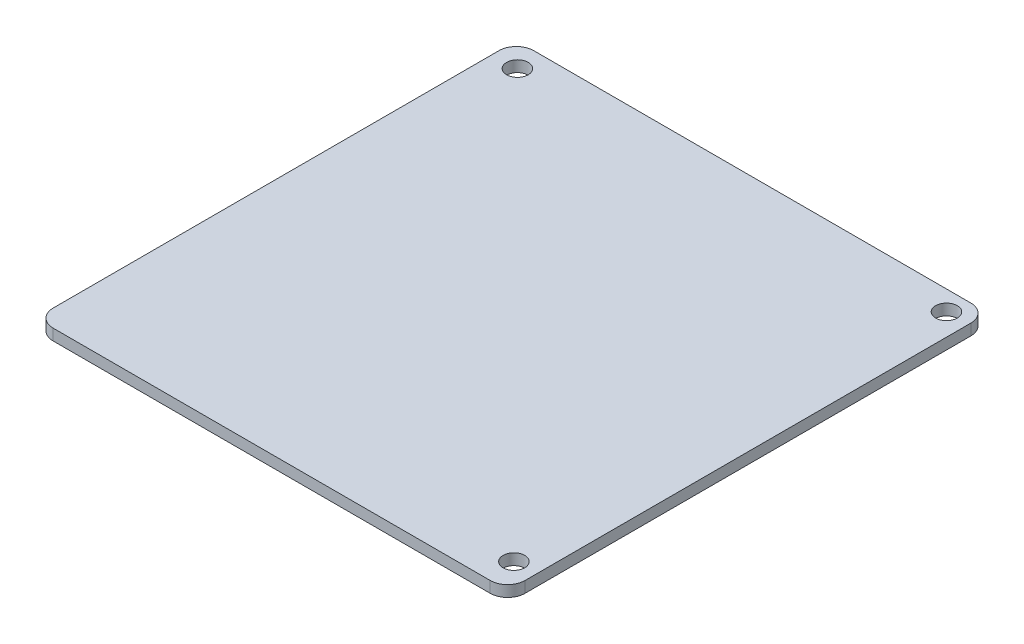
SolidWorks part; units mm, degrees
ref_plane "Front Plane" through (0, 0, 0) normal (0, 0, 1) x (1, 0, 0)
ref_plane "Top Plane" through (0, 0, 0) normal (0, 1, 0) x (1, 0, 0)
ref_plane "Right Plane" through (0, 0, 0) normal (1, 0, 0) x (0, 0, -1)
sketch "Sketch1" plane through (0, 0, 0) normal (0, 1, 0) x (1, 0, 0)
  line L0 (-31.334, 31.96) -> (31.334, 31.96) construction
  line L1 (-33.874, -34.5) -> (33.874, -34.5)
  line L2 (-33.874, -34.5) -> (-33.874, 34.5)
  line L3 (-33.874, 34.5) -> (33.874, 34.5)
  line L4 (33.874, -34.5) -> (33.874, 34.5)
  line L5 (-33.874, -34.5) -> (33.874, 34.5) construction
  line L6 (-33.874, 34.5) -> (33.874, -34.5) construction
  line L7 (31.334, -31.96) -> (31.334, 31.96) construction
  line L8 (-31.334, -31.96) -> (31.334, -31.96) construction
  line L9 (-31.334, -31.96) -> (-31.334, 31.96) construction
  point P0 (0, 0)
  dimension "D1" = 69
  dimension "D2" = 67.748
  dimension "D3" = 2.54
extrude "Boss-Extrude1" add sketch "Sketch1" along normal blind 1.6
sketch "Sketch2" plane through (0, 1.6, 0) normal (0, 1, 0) x (1, 0, 0)
  line L0 (-30.323, 34.5) -> (-30.323, 31.1) construction
  line L1 (33.874, 34.5) -> (-33.874, 34.5) construction
  line L2 (-33.874, 31.1) -> (-30.323, 31.1) construction
  line L3 (-33.874, 34.5) -> (-33.874, -34.5) construction
  line L4 (30.727, 34.5) -> (30.727, 31.65) construction
  line L5 (30.727, 31.65) -> (33.874, 31.65) construction
  line L6 (33.874, -34.5) -> (33.874, 34.5) construction
  line L7 (30.724, -34.5) -> (30.724, -30.453) construction
  line L8 (-33.874, -34.5) -> (33.874, -34.5) construction
  line L9 (30.724, -30.453) -> (33.874, -30.453) construction
  point P1 (-30.323, 31.1)
  point P8 (30.727, 31.65)
  point P13 (30.724, -30.453)
  point P27 (-30.323, 31.1)
  point P29 (30.727, 31.65)
  point P31 (30.724, -30.453)
  dimension "D1" = 3.4
  dimension "D2" = 3.551
  dimension "D3" = 2.85
  dimension "D4" = 3.147
  dimension "D5" = 3.15
  dimension "D6" = 4.047
hole_wizard "M2.5 Clearance Hole2" positions "Sketch2" profile "Sketch3" hole size "M2.5" standard "ANSI Metric"
sketch "Sketch3" plane through (30.724, 1.6, 30.453) normal (1, 0, 0) x (0, 0, 1)
  line L0 (0, 0) -> (0, 51.7313)
  line L1 (0, 51.7313) -> (1.55, 50.8)
  line L2 (1.55, 50.8) -> (1.55, 0)
  line L5 (1.55, 0) -> (0, 0)
  line L10 (0, 51.7313) -> (-1.55, 50.8) construction
  line L11 (0, -6.35) -> (0, 107.95) construction
  dimension "Hole Dia." = 3.1
  dimension "Hole Depth" = 50.8
  dimension "Drill Angle" = 118
fillet "Fillet1" radius 2.5 4 edges at (-33.874, 0.8, 34.5) (33.874, 0.8, 34.5) (33.874, 0.8, -34.5) (-33.874, 0.8, -34.5)
